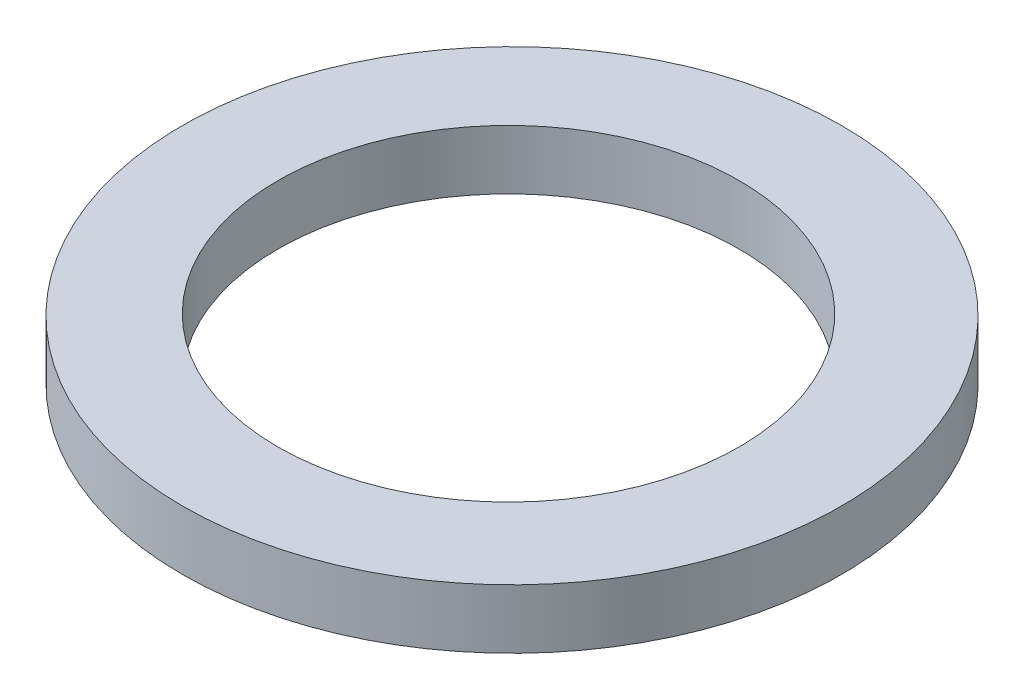
SolidWorks part; units mm, degrees
ref_plane "Front Plane" through (0, 0, 0) normal (0, 0, 1) x (1, 0, 0)
ref_plane "Top Plane" through (0, 0, 0) normal (0, 1, 0) x (1, 0, 0)
ref_plane "Right Plane" through (0, 0, 0) normal (1, 0, 0) x (0, 0, -1)
sketch "Sketch1" plane through (0, 0, 0) normal (0, 1, 0) x (1, 0, 0)
  circle A0 centre (0, 0) radius 17.78
  circle A1 centre (0.2682, 0) radius 25.4
  dimension "D1" = 35.56
  dimension "D2" = 50.8
extrude "Boss-Extrude1" add sketch "Sketch1" along normal blind 4.572
